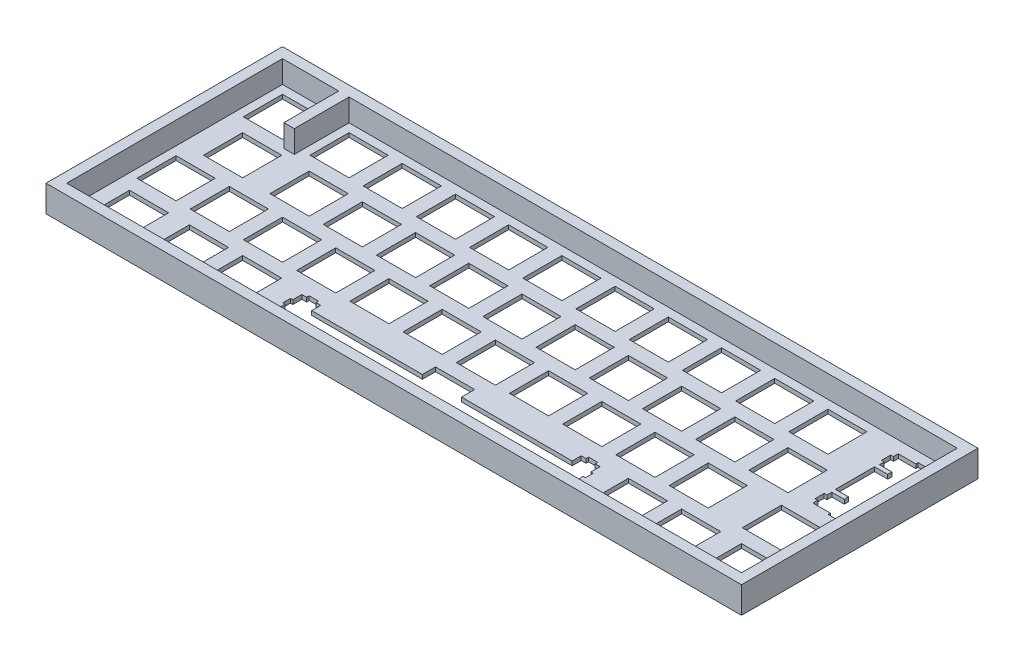
SolidWorks part; units mm, degrees
ref_plane "Plan de face" through (0, 0, 0) normal (0, 0, 1) x (1, 0, 0)
ref_plane "Plan de dessus" through (0, 0, 0) normal (0, 1, 0) x (1, 0, 0)
ref_plane "Plan de droite" through (0, 0, 0) normal (1, 0, 0) x (0, 0, -1)
sketch "Esquisse2" plane through (0, 0, 0) normal (0, 1, 0) x (1, 0, 0)
  line L0 (-4.1403, 80.6931) -> (244.835, 80.6931)
  line L1 (244.835, 80.6931) -> (244.835, -3.9764)
  line L2 (244.835, -3.9764) -> (-4.1403, -3.9764)
  line L3 (-4.1403, -3.9764) -> (-4.1403, 80.6931)
  line L4 (114.537, 16.7831) -> (114.537, 12.0826)
  line L5 (114.537, 12.0826) -> (74.9131, 12.0826)
  line L6 (74.9131, 12.0826) -> (74.9131, 15.3128)
  line L7 (74.9131, 15.3128) -> (73.1876, 15.3128)
  line L8 (73.1876, 15.3128) -> (73.1876, 16.2347)
  line L9 (73.1876, 16.2347) -> (69.887, 16.2347)
  line L10 (69.887, 16.2347) -> (69.887, 15.3128)
  line L11 (69.887, 15.3128) -> (68.162, 15.3128)
  line L12 (68.162, 15.3128) -> (68.162, 12.0826)
  line L13 (68.162, 12.0826) -> (67.3379, 12.0826)
  line L14 (67.3379, 12.0826) -> (67.3379, 9.2838)
  line L15 (67.3379, 9.2838) -> (68.162, 9.2838)
  line L16 (68.162, 9.2838) -> (68.162, 3.0138)
  line L17 (68.162, 3.0138) -> (69.887, 3.0138)
  line L18 (69.887, 3.0138) -> (69.887, 2.0326)
  line L19 (69.887, 2.0326) -> (73.1876, 2.0326)
  line L20 (73.1876, 2.0326) -> (73.1876, 3.0138)
  line L21 (73.1876, 3.0138) -> (74.9131, 3.0138)
  line L22 (74.9131, 3.0138) -> (74.9131, 7.4827)
  line L23 (74.9131, 7.4827) -> (114.537, 7.4827)
  line L24 (114.537, 7.4827) -> (114.537, 2.7836)
  line L25 (114.537, 2.7836) -> (128.538, 2.7836)
  line L26 (128.538, 2.7836) -> (128.538, 7.4827)
  line L27 (128.538, 7.4827) -> (168.162, 7.4827)
  line L28 (168.162, 7.4827) -> (168.162, 3.0138)
  line L29 (168.162, 3.0138) -> (169.887, 3.0138)
  line L30 (169.887, 3.0138) -> (169.887, 2.0326)
  line L31 (169.887, 2.0326) -> (173.188, 2.0326)
  line L32 (173.188, 2.0326) -> (173.188, 3.0138)
  line L33 (173.188, 3.0138) -> (174.913, 3.0138)
  line L34 (174.913, 3.0138) -> (174.913, 9.2838)
  line L35 (174.913, 9.2838) -> (175.737, 9.2838)
  line L36 (175.737, 9.2838) -> (175.737, 12.0826)
  line L37 (175.737, 12.0826) -> (174.913, 12.0826)
  line L38 (174.913, 12.0826) -> (174.913, 15.3128)
  line L39 (174.913, 15.3128) -> (173.188, 15.3128)
  line L40 (173.188, 15.3128) -> (173.188, 16.2347)
  line L41 (173.188, 16.2347) -> (169.887, 16.2347)
  line L42 (169.887, 16.2347) -> (169.887, 15.3128)
  line L43 (169.887, 15.3128) -> (168.162, 15.3128)
  line L44 (168.162, 15.3128) -> (168.162, 12.0826)
  line L45 (168.162, 12.0826) -> (128.538, 12.0826)
  line L46 (128.538, 12.0826) -> (128.538, 16.7831)
  line L47 (128.538, 16.7831) -> (114.537, 16.7831)
  line L48 (224.076, 16.7831) -> (238.075, 16.7831)
  line L49 (238.075, 16.7831) -> (238.075, 2.7836)
  line L50 (238.075, 2.7836) -> (224.076, 2.7836)
  line L51 (224.076, 2.7836) -> (224.076, 16.7831)
  line L52 (202.645, 16.7831) -> (216.644, 16.7831)
  line L53 (216.644, 16.7831) -> (216.644, 2.7836)
  line L54 (216.644, 2.7836) -> (202.645, 2.7836)
  line L55 (202.645, 2.7836) -> (202.645, 16.7831)
  line L56 (183.595, 16.7831) -> (197.594, 16.7831)
  line L57 (197.594, 16.7831) -> (197.594, 2.7836)
  line L58 (197.594, 2.7836) -> (183.595, 2.7836)
  line L59 (183.595, 2.7836) -> (183.595, 16.7831)
  line L60 (45.4822, 16.7831) -> (59.4815, 16.7831)
  line L61 (59.4815, 16.7831) -> (59.4815, 2.7836)
  line L62 (59.4815, 2.7836) -> (45.4822, 2.7836)
  line L63 (45.4822, 2.7836) -> (45.4822, 16.7831)
  line L64 (26.4322, 16.7831) -> (40.4315, 16.7831)
  line L65 (40.4315, 16.7831) -> (40.4315, 2.7836)
  line L66 (40.4315, 2.7836) -> (26.4322, 2.7836)
  line L67 (26.4322, 2.7836) -> (26.4322, 16.7831)
  line L68 (5.0009, 16.7831) -> (19.0004, 16.7831)
  line L69 (19.0004, 16.7831) -> (19.0004, 2.7836)
  line L70 (19.0004, 2.7836) -> (5.0009, 2.7836)
  line L71 (5.0009, 2.7836) -> (5.0009, 16.7831)
  line L72 (219.312, 35.833) -> (233.313, 35.833)
  line L73 (233.313, 35.833) -> (233.313, 21.8336)
  line L74 (233.313, 21.8336) -> (219.312, 21.8336)
  line L75 (219.312, 21.8336) -> (219.312, 35.833)
  line L76 (193.12, 35.833) -> (207.119, 35.833)
  line L77 (207.119, 35.833) -> (207.119, 21.8336)
  line L78 (207.119, 21.8336) -> (193.12, 21.8336)
  line L79 (193.12, 21.8336) -> (193.12, 35.833)
  line L80 (174.07, 35.833) -> (188.069, 35.833)
  line L81 (188.069, 35.833) -> (188.069, 21.8336)
  line L82 (188.069, 21.8336) -> (174.07, 21.8336)
  line L83 (174.07, 21.8336) -> (174.07, 35.833)
  line L84 (155.02, 35.833) -> (169.019, 35.833)
  line L85 (169.019, 35.833) -> (169.019, 21.8336)
  line L86 (169.019, 21.8336) -> (155.02, 21.8336)
  line L87 (155.02, 21.8336) -> (155.02, 35.833)
  line L88 (135.97, 35.833) -> (149.969, 35.833)
  line L89 (149.969, 35.833) -> (149.969, 21.8336)
  line L90 (149.969, 21.8336) -> (135.97, 21.8336)
  line L91 (135.97, 21.8336) -> (135.97, 35.833)
  line L92 (116.918, 35.833) -> (130.919, 35.833)
  line L93 (130.919, 35.833) -> (130.919, 21.8336)
  line L94 (130.919, 21.8336) -> (116.918, 21.8336)
  line L95 (116.918, 21.8336) -> (116.918, 35.833)
  line L96 (97.8683, 35.833) -> (111.869, 35.833)
  line L97 (111.869, 35.833) -> (111.869, 21.8336)
  line L98 (111.869, 21.8336) -> (97.8683, 21.8336)
  line L99 (97.8683, 21.8336) -> (97.8683, 35.833)
  line L100 (78.8197, 35.833) -> (92.819, 35.833)
  line L101 (92.819, 35.833) -> (92.819, 21.8336)
  line L102 (92.819, 21.8336) -> (78.8197, 21.8336)
  line L103 (78.8197, 21.8336) -> (78.8197, 35.833)
  line L104 (59.7697, 35.833) -> (73.769, 35.833)
  line L105 (73.769, 35.833) -> (73.769, 21.8336)
  line L106 (73.769, 21.8336) -> (59.7697, 21.8336)
  line L107 (59.7697, 21.8336) -> (59.7697, 35.833)
  line L108 (40.7197, 35.833) -> (54.719, 35.833)
  line L109 (54.719, 35.833) -> (54.719, 21.8336)
  line L110 (54.719, 21.8336) -> (40.7197, 21.8336)
  line L111 (40.7197, 21.8336) -> (40.7197, 35.833)
  line L112 (21.6697, 35.833) -> (35.669, 35.833)
  line L113 (35.669, 35.833) -> (35.669, 21.8336)
  line L114 (35.669, 21.8336) -> (21.6697, 21.8336)
  line L115 (21.6697, 21.8336) -> (21.6697, 35.833)
  line L116 (2.6197, 35.833) -> (16.6192, 35.833)
  line L117 (16.6192, 35.833) -> (16.6192, 21.8336)
  line L118 (16.6192, 21.8336) -> (2.6197, 21.8336)
  line L119 (2.6197, 21.8336) -> (2.6197, 35.833)
  line L120 (202.645, 54.8831) -> (216.644, 54.8831)
  line L121 (216.644, 54.8831) -> (216.644, 40.8838)
  line L122 (216.644, 40.8838) -> (202.645, 40.8838)
  line L123 (202.645, 40.8838) -> (202.645, 54.8831)
  line L124 (183.595, 54.8831) -> (197.594, 54.8831)
  line L125 (197.594, 54.8831) -> (197.594, 40.8838)
  line L126 (197.594, 40.8838) -> (183.595, 40.8838)
  line L127 (183.595, 40.8838) -> (183.595, 54.8831)
  line L128 (164.545, 54.8831) -> (178.544, 54.8831)
  line L129 (178.544, 54.8831) -> (178.544, 40.8838)
  line L130 (178.544, 40.8838) -> (164.545, 40.8838)
  line L131 (164.545, 40.8838) -> (164.545, 54.8831)
  line L132 (145.495, 54.8831) -> (159.494, 54.8831)
  line L133 (159.494, 54.8831) -> (159.494, 40.8838)
  line L134 (159.494, 40.8838) -> (145.495, 40.8838)
  line L135 (145.495, 40.8838) -> (145.495, 54.8831)
  line L136 (126.445, 54.8831) -> (140.444, 54.8831)
  line L137 (140.444, 54.8831) -> (140.444, 40.8838)
  line L138 (140.444, 40.8838) -> (126.445, 40.8838)
  line L139 (126.445, 40.8838) -> (126.445, 54.8831)
  line L140 (107.395, 54.8831) -> (121.394, 54.8831)
  line L141 (121.394, 54.8831) -> (121.394, 40.8838)
  line L142 (121.394, 40.8838) -> (107.395, 40.8838)
  line L143 (107.395, 40.8838) -> (107.395, 54.8831)
  line L144 (88.3447, 54.8831) -> (102.344, 54.8831)
  line L145 (102.344, 54.8831) -> (102.344, 40.8838)
  line L146 (102.344, 40.8838) -> (88.3447, 40.8838)
  line L147 (88.3447, 40.8838) -> (88.3447, 54.8831)
  line L148 (69.2947, 54.8831) -> (83.294, 54.8831)
  line L149 (83.294, 54.8831) -> (83.294, 40.8838)
  line L150 (83.294, 40.8838) -> (69.2947, 40.8838)
  line L151 (69.2947, 40.8838) -> (69.2947, 54.8831)
  line L152 (50.2447, 54.8831) -> (64.244, 54.8831)
  line L153 (64.244, 54.8831) -> (64.244, 40.8838)
  line L154 (64.244, 40.8838) -> (50.2447, 40.8838)
  line L155 (50.2447, 40.8838) -> (50.2447, 54.8831)
  line L156 (31.1947, 54.8831) -> (45.194, 54.8831)
  line L157 (45.194, 54.8831) -> (45.194, 40.8838)
  line L158 (45.194, 40.8838) -> (31.1947, 40.8838)
  line L159 (31.1947, 40.8838) -> (31.1947, 54.8831)
  line L160 (7.3822, 54.8831) -> (21.3817, 54.8831)
  line L161 (21.3817, 54.8831) -> (21.3817, 40.8838)
  line L162 (21.3817, 40.8838) -> (7.3822, 40.8838)
  line L163 (7.3822, 40.8838) -> (7.3822, 54.8831)
  line L164 (230.576, 73.5087) -> (230.576, 72.6832)
  line L165 (230.576, 72.6832) -> (224.306, 72.6832)
  line L166 (224.306, 72.6832) -> (224.306, 70.9581)
  line L167 (224.306, 70.9581) -> (223.325, 70.9581)
  line L168 (223.325, 70.9581) -> (223.325, 67.6589)
  line L169 (223.325, 67.6589) -> (224.306, 67.6589)
  line L170 (224.306, 67.6589) -> (224.306, 65.9335)
  line L171 (224.306, 65.9335) -> (228.775, 65.9335)
  line L172 (228.775, 65.9335) -> (228.775, 64.4081)
  line L173 (228.775, 64.4081) -> (224.076, 64.4081)
  line L174 (224.076, 64.4081) -> (224.076, 50.4088)
  line L175 (224.076, 50.4088) -> (228.775, 50.4088)
  line L176 (228.775, 50.4088) -> (228.775, 48.883)
  line L177 (228.775, 48.883) -> (224.306, 48.883)
  line L178 (224.306, 48.883) -> (224.306, 47.1579)
  line L179 (224.306, 47.1579) -> (223.325, 47.1579)
  line L180 (223.325, 47.1579) -> (223.325, 43.8587)
  line L181 (223.325, 43.8587) -> (224.306, 43.8587)
  line L182 (224.306, 43.8587) -> (224.306, 42.1337)
  line L183 (224.306, 42.1337) -> (230.576, 42.1337)
  line L184 (230.576, 42.1337) -> (230.576, 41.3082)
  line L185 (230.576, 41.3082) -> (233.375, 41.3082)
  line L186 (233.375, 41.3082) -> (233.375, 42.1337)
  line L187 (233.375, 42.1337) -> (236.605, 42.1337)
  line L188 (236.605, 42.1337) -> (236.605, 43.8587)
  line L189 (236.605, 43.8587) -> (237.526, 43.8587)
  line L190 (237.526, 43.8587) -> (237.526, 47.1579)
  line L191 (237.526, 47.1579) -> (236.605, 47.1579)
  line L192 (236.605, 47.1579) -> (236.605, 48.883)
  line L193 (236.605, 48.883) -> (233.375, 48.883)
  line L194 (233.375, 48.883) -> (233.375, 50.4088)
  line L195 (233.375, 50.4088) -> (238.075, 50.4088)
  line L196 (238.075, 50.4088) -> (238.075, 64.4081)
  line L197 (238.075, 64.4081) -> (233.375, 64.4081)
  line L198 (233.375, 64.4081) -> (233.375, 65.9335)
  line L199 (233.375, 65.9335) -> (236.605, 65.9335)
  line L200 (236.605, 65.9335) -> (236.605, 67.6589)
  line L201 (236.605, 67.6589) -> (237.526, 67.6589)
  line L202 (237.526, 67.6589) -> (237.526, 70.9581)
  line L203 (237.526, 70.9581) -> (236.605, 70.9581)
  line L204 (236.605, 70.9581) -> (236.605, 72.6832)
  line L205 (236.605, 72.6832) -> (233.375, 72.6832)
  line L206 (233.375, 72.6832) -> (233.375, 73.5087)
  line L207 (233.375, 73.5087) -> (230.576, 73.5087)
  line L208 (197.882, 73.9331) -> (211.882, 73.9331)
  line L209 (211.882, 73.9331) -> (211.882, 59.9338)
  line L210 (211.882, 59.9338) -> (197.882, 59.9338)
  line L211 (197.882, 59.9338) -> (197.882, 73.9331)
  line L212 (178.832, 73.9331) -> (192.832, 73.9331)
  line L213 (192.832, 73.9331) -> (192.832, 59.9338)
  line L214 (192.832, 59.9338) -> (178.832, 59.9338)
  line L215 (178.832, 59.9338) -> (178.832, 73.9331)
  line L216 (159.782, 73.9331) -> (173.782, 73.9331)
  line L217 (173.782, 73.9331) -> (173.782, 59.9338)
  line L218 (173.782, 59.9338) -> (159.782, 59.9338)
  line L219 (159.782, 59.9338) -> (159.782, 73.9331)
  line L220 (140.732, 73.9331) -> (154.732, 73.9331)
  line L221 (154.732, 73.9331) -> (154.732, 59.9338)
  line L222 (154.732, 59.9338) -> (140.732, 59.9338)
  line L223 (140.732, 59.9338) -> (140.732, 73.9331)
  line L224 (121.682, 73.9331) -> (135.682, 73.9331)
  line L225 (135.682, 73.9331) -> (135.682, 59.9338)
  line L226 (135.682, 59.9338) -> (121.682, 59.9338)
  line L227 (121.682, 59.9338) -> (121.682, 73.9331)
  line L228 (102.632, 73.9331) -> (116.632, 73.9331)
  line L229 (116.632, 73.9331) -> (116.632, 59.9338)
  line L230 (116.632, 59.9338) -> (102.632, 59.9338)
  line L231 (102.632, 59.9338) -> (102.632, 73.9331)
  line L232 (83.5822, 73.9331) -> (97.5815, 73.9331)
  line L233 (97.5815, 73.9331) -> (97.5815, 59.9338)
  line L234 (97.5815, 59.9338) -> (83.5822, 59.9338)
  line L235 (83.5822, 59.9338) -> (83.5822, 73.9331)
  line L236 (64.5322, 73.9331) -> (78.5315, 73.9331)
  line L237 (78.5315, 73.9331) -> (78.5315, 59.9338)
  line L238 (78.5315, 59.9338) -> (64.5322, 59.9338)
  line L239 (64.5322, 59.9338) -> (64.5322, 73.9331)
  line L240 (45.4822, 73.9331) -> (59.4815, 73.9331)
  line L241 (59.4815, 73.9331) -> (59.4815, 59.9338)
  line L242 (59.4815, 59.9338) -> (45.4822, 59.9338)
  line L243 (45.4822, 59.9338) -> (45.4822, 73.9331)
  line L244 (26.4322, 73.9331) -> (40.4315, 73.9331)
  line L245 (40.4315, 73.9331) -> (40.4315, 59.9338)
  line L246 (40.4315, 59.9338) -> (26.4322, 59.9338)
  line L247 (26.4322, 59.9338) -> (26.4322, 73.9331)
  line L248 (2.6197, 73.9331) -> (16.6192, 73.9331)
  line L249 (16.6192, 73.9331) -> (16.6192, 59.9338)
  line L250 (16.6192, 59.9338) -> (2.6197, 59.9338)
  line L251 (2.6197, 59.9338) -> (2.6197, 73.9331)
  dimension "D1" = 13.9995
  dimension "D2" = 13.9993
  dimension "D3" = 13.9995
  dimension "D4" = 13.999
  dimension "D5" = 6.76
  dimension "D6" = 6.76
  dimension "D7" = 6.76
  dimension "D8" = 6.76
extrude "Boss.-Extru.1" add sketch "Esquisse2" along normal blind 1.5
sketch "Esquisse4" plane through (0, 1.5, 0) normal (0, 1, 0) x (1, 0, 0)
  line L0 (26.4322, 73.9331) -> (26.4322, 59.9338) construction
  line L1 (-4.1403, 80.6931) -> (244.835, 80.6931)
  line L2 (-4.1403, 80.6931) -> (-4.1403, -3.9764)
  line L3 (-4.1403, -3.9764) -> (244.835, -3.9764)
  line L4 (244.835, 80.6931) -> (244.835, -3.9764)
  line L5 (-0.4303, 76.9831) -> (19.6692, 76.9831)
  line L6 (-0.4303, 76.9831) -> (-0.4303, -0.2664)
  line L7 (-0.4303, -0.2664) -> (241.125, -0.2664)
  line L8 (241.125, 76.9831) -> (241.125, -0.2664)
  line L10 (19.6692, 76.9831) -> (19.6692, 57.3831)
  line L11 (19.6692, 57.3831) -> (23.3822, 57.3831)
  line L12 (23.3822, 76.9831) -> (23.3822, 57.3831)
  line L13 (16.6192, 59.9338) -> (16.6192, 73.9331) construction
  line L14 (23.3822, 76.9831) -> (241.125, 76.9831)
  dimension "D1" = 3.71
  dimension "D2" = 3.71
  dimension "D3" = 3.71
  dimension "D4" = 3.71
  dimension "D5" = 3.05
  dimension "D6" = 3.05
  dimension "D7" = 19.6
extrude "Boss.-Extru.2" add sketch "Esquisse4" along normal blind 8
